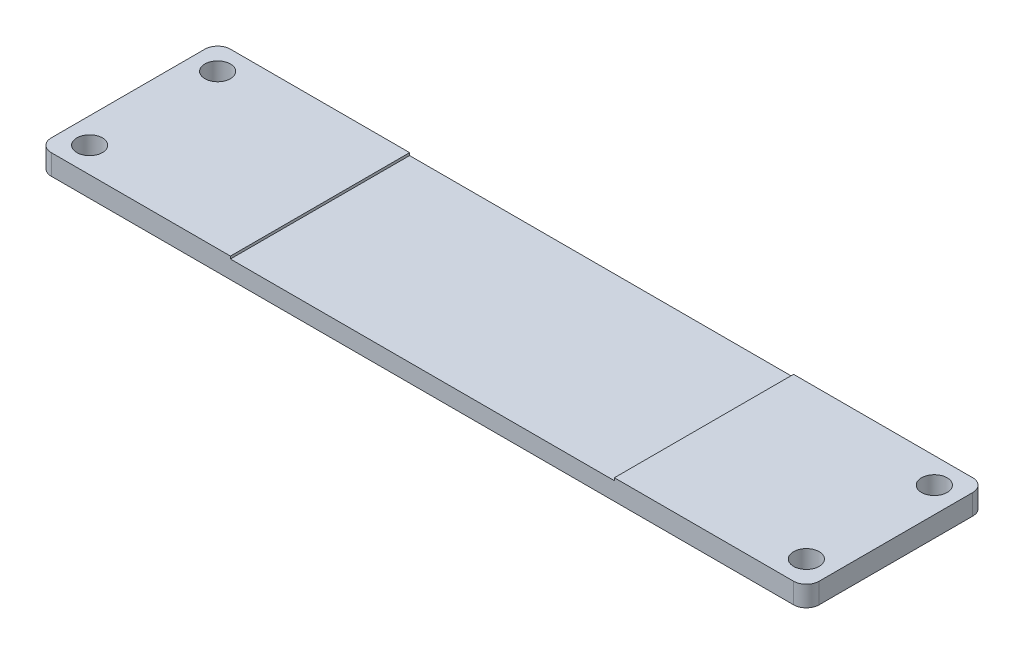
SolidWorks part; units mm, degrees
ref_plane "Front" through (0, 0, 0) normal (0, 0, 1) x (1, 0, 0)
ref_plane "Top" through (0, 0, 0) normal (0, 1, 0) x (1, 0, 0)
ref_plane "Right" through (0, 0, 0) normal (1, 0, 0) x (0, 0, -1)
sketch "草图1" plane through (0, 0, 0) normal (0, 1, 0) x (1, 0, 0)
  line L1 (15, -3.5) -> (-15, -3.5)
  line L2 (15, -3.5) -> (15, 3.5)
  line L3 (15, 3.5) -> (-15, 3.5)
  line L4 (-15, -3.5) -> (-15, 3.5)
  line L5 (15, -3.5) -> (-15, 3.5) construction
  line L6 (15, 3.5) -> (-15, -3.5) construction
  point P0 (0, 0)
  dimension "D1" = 30
  dimension "D2" = 7
extrude "凸台-拉伸1" add sketch "草图1" along normal blind 0.8
sketch "草图2" plane through (0, 0.8, 0) normal (0, 1, 0) x (1, 0, 0)
  line L0 (0, 9.719) -> (0, -5.4537) construction
  line L1 (-17.3542, 0) -> (19.1449, 0) construction
  line L2 (15, 3.5) -> (-15, 3.5) construction
  line L3 (-15, 3.5) -> (-15, -3.5) construction
  circle A0 centre (-14, 2.5) radius 0.5
  circle A1 centre (14, 2.5) radius 0.5
  circle A2 centre (14, -2.5) radius 0.5
  circle A3 centre (-14, -2.5) radius 0.5
  dimension "D1" = 1
  dimension "D2" = 1
  dimension "D3" = 1
  dimension "D4" = 28
  dimension "D5" = 5
extrude "切除-拉伸1" cut sketch "草图2" against normal through all
fillet "圆角1" radius 0.5 4 edges at (-15, 0.4, 3.5) (15, 0.4, 3.5) (15, 0.4, -3.5) (-15, 0.4, -3.5)
sketch "草图3" plane through (0, 0.8, 0) normal (0, 1, 0) x (1, 0, 0)
  line L1 (7.5, -3.5) -> (-7.5, -3.5)
  line L2 (7.5, -3.5) -> (7.5, 3.5)
  line L3 (7.5, 3.5) -> (-7.5, 3.5)
  line L4 (-7.5, -3.5) -> (-7.5, 3.5)
  line L5 (7.5, -3.5) -> (-7.5, 3.5) construction
  line L6 (7.5, 3.5) -> (-7.5, -3.5) construction
  point P0 (0, 0)
  dimension "D1" = 15
  dimension "D2" = 7
extrude "切除-拉伸2" cut sketch "草图3" against normal blind 0.1
